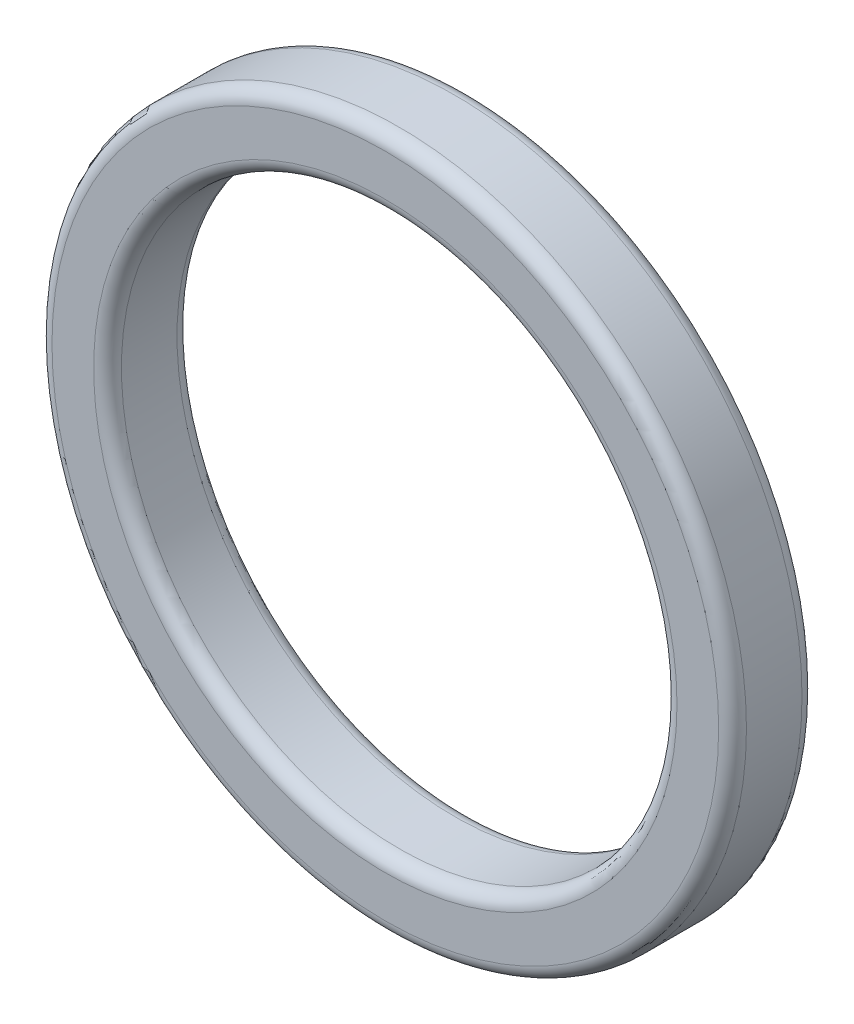
SolidWorks part; units mm, degrees
ref_plane "正面" through (0, 0, 0) normal (0, 0, 1) x (1, 0, 0)
ref_plane "平面" through (0, 0, 0) normal (0, 1, 0) x (1, 0, 0)
ref_plane "右側面" through (0, 0, 0) normal (1, 0, 0) x (0, 0, -1)
sketch "ｽｹｯﾁ1" plane through (0, 0, 0) normal (0, 0, 1) x (1, 0, 0)
  circle A0 centre (0, 0) radius 25
  circle A1 centre (0, 0) radius 20
  dimension "D1" = 40
  dimension "D2" = 50
extrude "ﾎﾞｽ - 押し出し1" add sketch "ｽｹｯﾁ1" along normal blind 6
fillet "ﾌｨﾚｯﾄ1" radius 1 4 edges at (20, 0, 0) (20, 0, 6) (25, 0, 0) (25, 0, 6)
